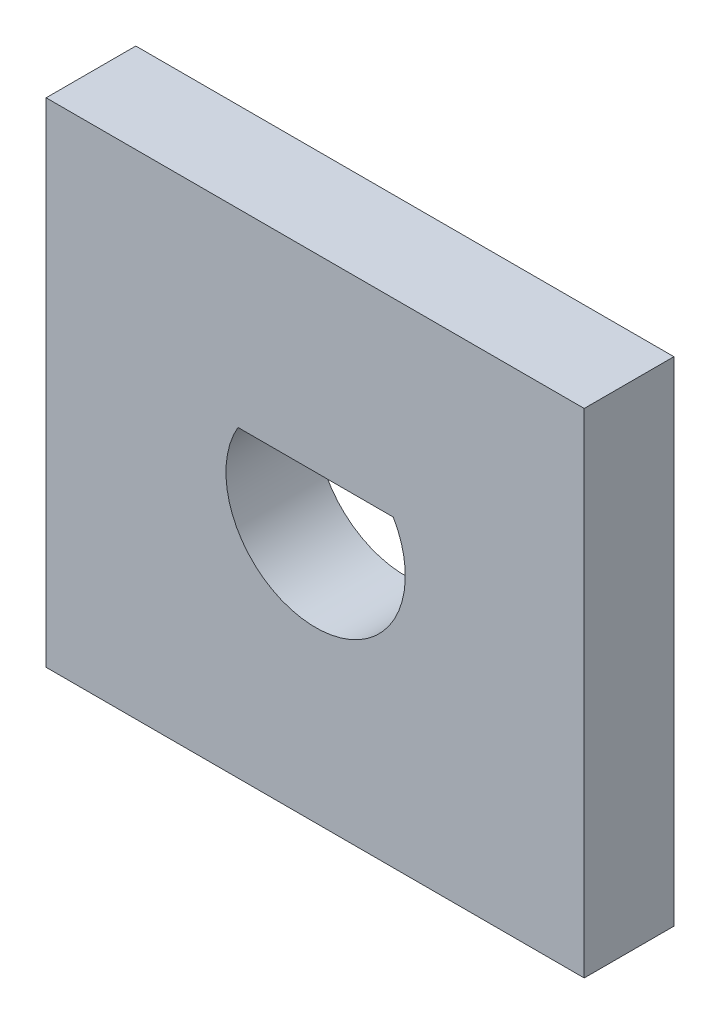
SolidWorks part; units mm, degrees
ref_plane "前视基准面" through (0, 0, 0) normal (0, 0, 1) x (1, 0, 0)
ref_plane "上视基准面" through (0, 0, 0) normal (0, 1, 0) x (1, 0, 0)
ref_plane "右视基准面" through (0, 0, 0) normal (1, 0, 0) x (0, 0, -1)
sketch "草图1" plane through (0, 0, 0) normal (0, 0, 1) x (1, 0, 0)
  line L1 (-6.0103, 5.2271) -> (5.9897, 5.2271)
  line L2 (-6.0103, 5.2271) -> (-6.0103, -5.7729)
  line L3 (-6.0103, -5.7729) -> (5.9897, -5.7729)
  line L4 (5.9897, 5.2271) -> (5.9897, -5.7729)
  dimension "D1" = 12
  dimension "D2" = 11
extrude "凸台-拉伸1" add sketch "草图1" along normal blind 2 contours L2 L3 L4 L1
sketch "草图2" plane through (0, 0, 2) normal (0, 0, 1) x (1, 0, 0)
  line L0 (0, 0) -> (0, 1)
  line L1 (-1.7321, 1) -> (1.7321, 1)
  circle A0 centre (0, 0) radius 2
  dimension "D1" = 1
extrude "切除-拉伸2" cut sketch "草图2" against normal blind 2
